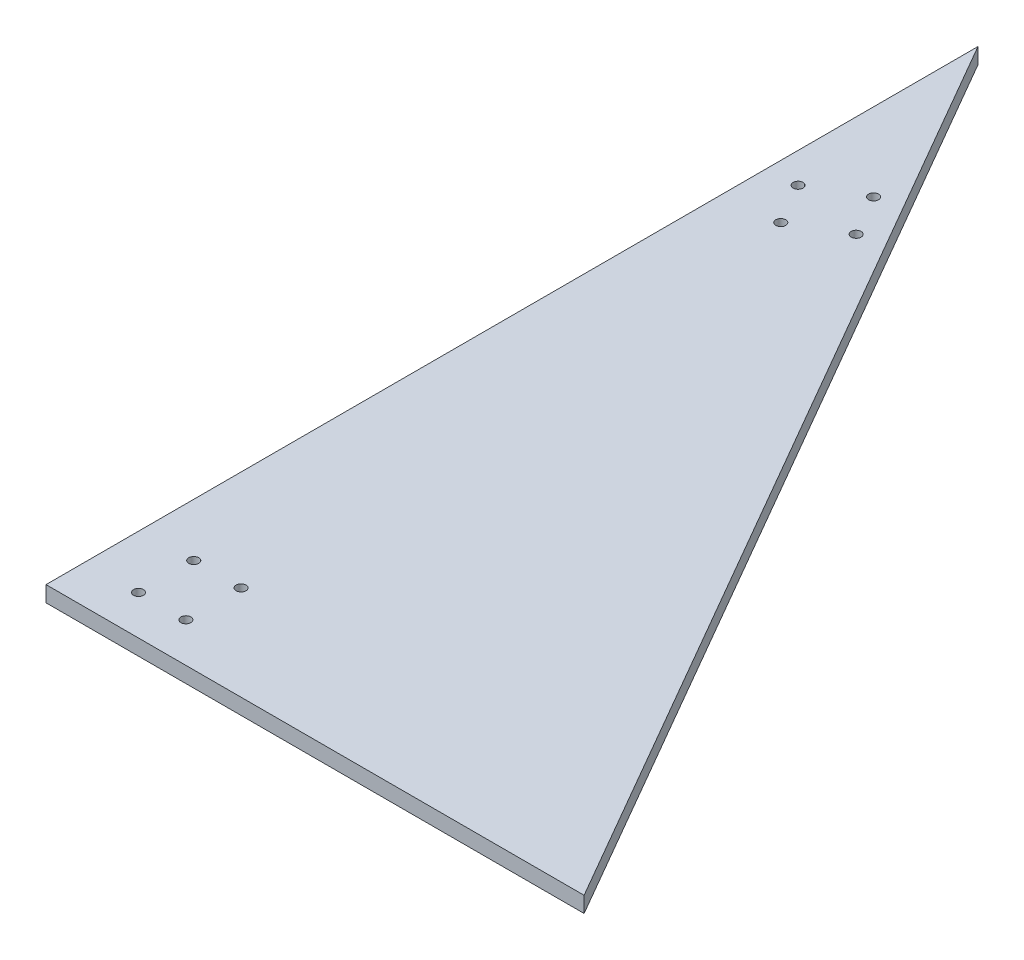
SolidWorks part; units mm, degrees
material "Oak"
ref_plane "Front" through (0, 0, 0) normal (0, 0, 1) x (1, 0, 0)
ref_plane "Top" through (0, 0, 0) normal (0, 1, 0) x (1, 0, 0)
ref_plane "Right" through (0, 0, 0) normal (1, 0, 0) x (0, 0, -1)
sketch "Sketch1" plane through (0, 0, 0) normal (0, 1, 0) x (1, 0, 0)
  line L0 (0, 0) -> (216.51, 0)
  line L1 (216.51, 0) -> (0, 375)
  line L2 (0, 375) -> (0, 0)
  dimension "D1" = 375
  dimension "D2" = 216.51
extrude "Boss-Extrude1" add sketch "Sketch1" along normal blind 6.35
hole_wizard "Ø4.0 (4) Diameter Hole1" positions "Sketch2" profile "Sketch3" hole size "Ø4.0" standard "ANSI Metric"
sketch "Sketch2" plane through (31.7572, 6.35, -326.3457) normal (0, 1, 0) x (0.5, 0, 0.866)
  point P0 (21.2724, -34.925)
  point P3 (40.3224, -12.7)
  point P6 (244.4233, -153.1376)
  point P9 (273.1958, -147.7525)
sketch "Sketch3" plane through (12.1478, 6.35, -290.4606) normal (1, 0, 0) x (0, 0, 1)
  line L0 (0, 0) -> (0, 11.2017)
  line L1 (0, 11.2017) -> (2, 10)
  line L2 (2, 10) -> (2, 0)
  line L3 (2, 0) -> (0, 0)
  line L4 (0, 11.2017) -> (-2, 10) construction
  line L5 (0, -6.35) -> (0, 107.95) construction
  dimension "Hole Dia." = 4
  dimension "Hole Depth" = 10
  dimension "Drill Angle" = 118
hole_wizard "Ø4.0 (4) Diameter Hole2" positions "Sketch4" profile "Sketch5" hole size "Ø4.0" standard "ANSI Metric"
sketch "Sketch4" plane through (31.7572, 0, -326.3457) normal (0, -1, 0) x (-0.5, 0, -0.866)
  point P0 (-21.2724, -12.7)
  point P3 (-40.3224, -34.925)
  point P6 (-253.9485, -136.6399)
  point P9 (-263.6707, -164.2502)
sketch "Sketch5" plane through (31.3951, 0, -301.5733) normal (1, 0, 0) x (0, 0, -1)
  line L0 (0, 0) -> (0, 11.2017)
  line L1 (0, 11.2017) -> (2, 10)
  line L2 (2, 10) -> (2, 0)
  line L3 (2, 0) -> (0, 0)
  line L4 (0, 11.2017) -> (-2, 10) construction
  line L5 (0, -6.35) -> (0, 107.95) construction
  dimension "Hole Dia." = 4
  dimension "Hole Depth" = 10
  dimension "Drill Angle" = 118
